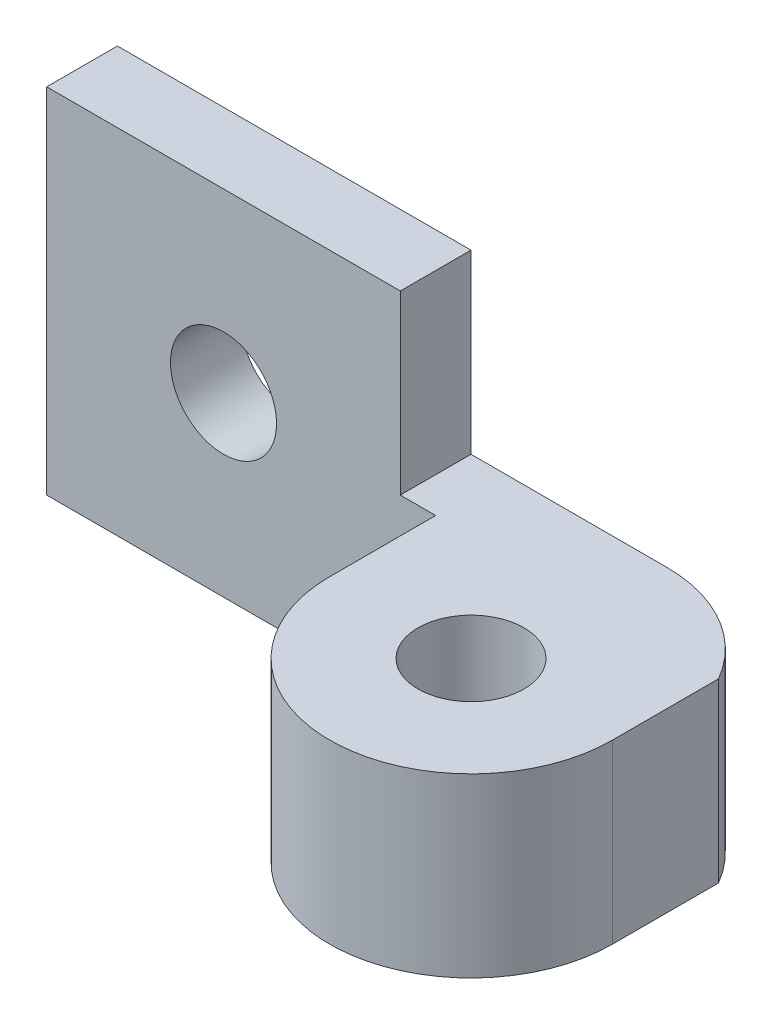
SolidWorks part; units mm, degrees
ref_plane "Front Plane" through (0, 0, 0) normal (0, 0, 1) x (1, 0, 0)
ref_plane "Top Plane" through (0, 0, 0) normal (0, 1, 0) x (1, 0, 0)
ref_plane "Right Plane" through (0, 0, 0) normal (1, 0, 0) x (0, 0, -1)
sketch "Esquisse1" plane through (0, 0, 0) normal (0, 0, 1) x (1, 0, 0)
  line L0 (0, 0) -> (15, 0)
  line L1 (0, 10) -> (10, 10)
  line L2 (10, 10) -> (10, 5)
  line L3 (15, 0) -> (15, 5)
  line L4 (10, 5) -> (15, 5)
  line L5 (0, 10) -> (0, 0)
  circle A0 centre (5, 5) radius 1.5
  point P8 (7.5014, 10)
  point P10 (0, 0)
  point P11 (5, 10)
  point P12 (0, 0)
  point P13 (0, 5)
  point P14 (9.9891, 10.4658)
  dimension "D5" = 3
  dimension "D1" = 10
  dimension "D2" = 5
  dimension "D3" = 15
  dimension "D4" = 10
extrude "Boss.-Extru.2" add sketch "Esquisse1" along normal blind 2
sketch "Esquisse4" plane through (0, 0, 0) normal (0, -1, 0) x (1, 0, 0)
  line L1 (15, 2) -> (15, 0) construction
  line L2 (11, 5) -> (11, 0)
  line L3 (0, 0) -> (15, 0) construction
  line L4 (19, 5) -> (19, 2)
  line L5 (11, 0) -> (15.5359, 0)
  line L7 (0, 2) -> (15, 2) construction
  arc A0 (19, 2) -> (15.5359, 0) centre (15.5359, 4) cw
  circle A1 centre (15, 5) radius 1.5
  arc A2 (11, 5) -> (19, 5) centre (15, 5) cw
  point P1 (17.1856, -0.1579)
  point P12 (16.5, 2.5)
  point P13 (0, 0)
  point P15 (11, -1.1491)
  point P16 (11, -0.1579)
  point P17 (0, 0)
  point P18 (19, 1.0811)
  point P21 (19, 4)
  point P22 (0, 0)
  point P23 (0, 0)
  point P24 (19, 1.9236)
  point P25 (0, 0)
  dimension "D1" = 4
  dimension "D2" = 3
  dimension "D3" = 3
  dimension "D4" = 4
extrude "Boss.-Extru.3" add sketch "Esquisse4" against normal blind 5
